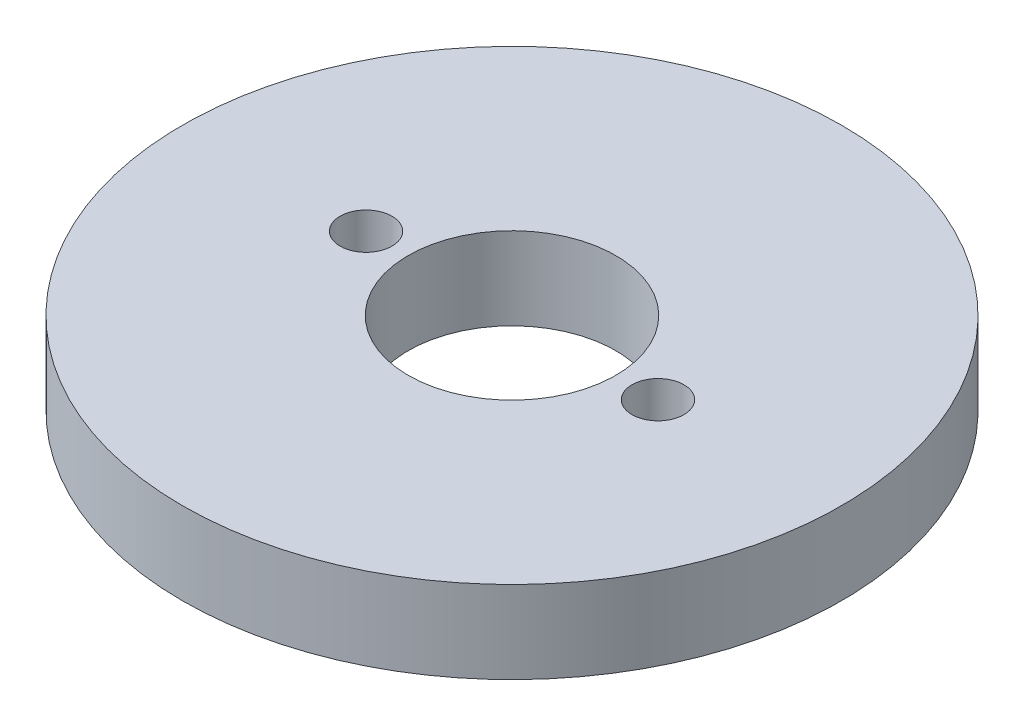
SolidWorks part; units mm, degrees
ref_plane "Front Plane" through (0, 0, 0) normal (0, 0, 1) x (1, 0, 0)
ref_plane "Top Plane" through (0, 0, 0) normal (0, 1, 0) x (1, 0, 0)
ref_plane "Right Plane" through (0, 0, 0) normal (1, 0, 0) x (0, 0, -1)
sketch "Sketch1" plane through (0, 0, 0) normal (0, 1, 0) x (1, 0, 0)
  circle A0 centre (0, 0) radius 50.8
  circle A1 centre (0, 0) radius 16
extrude "Boss-Extrude1" add sketch "Sketch1" along normal blind 12.7
sketch "Sketch2" plane through (0, 12.7, 0) normal (0, 1, 0) x (1, 0, 0)
  line L0 (0, 0) -> (22.5, 0)
  line L1 (0, 0) -> (-22.5, 0)
  circle A0 centre (-22.5, 0) radius 4
  circle A1 centre (22.5, 0) radius 4
  dimension "D1" = 22.5
  dimension "D2" = 22.5
extrude "Cut-Extrude1" cut sketch "Sketch2" against normal blind 12.7
